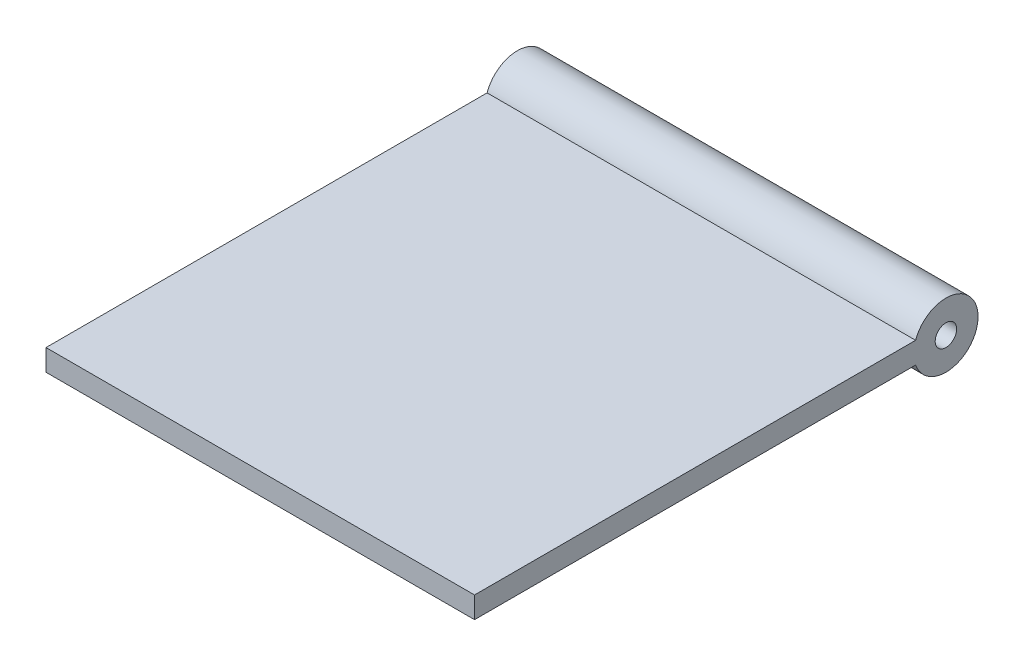
SolidWorks part; units mm, degrees
ref_plane "Front Plane" through (0, 0, 0) normal (0, 0, 1) x (1, 0, 0)
ref_plane "Top Plane" through (0, 0, 0) normal (0, 1, 0) x (1, 0, 0)
ref_plane "Right Plane" through (0, 0, 0) normal (1, 0, 0) x (0, 0, -1)
sketch "Sketch1" plane through (0, 0, 0) normal (1, 0, 0) x (0, 0, -1)
  line L9 (0, 2.5) -> (-110, 2.5)
  line L10 (0, 2.5) -> (0, -2.5)
  line L11 (0, -2.5) -> (-110, -2.5)
  line L12 (-110, 2.5) -> (-110, -2.5)
  circle A0 centre (0, 0) radius 7.5
  circle A1 centre (0, 0) radius 2.5
  dimension "D1" = 15
  dimension "D2" = 5
  dimension "D3" = 110
extrude "Boss-Extrude1" add sketch "Sketch1" along normal blind 100 contours A1 L11 A0 L9 | A1 L9 A0 L11 | A0 L9 L12 L11
